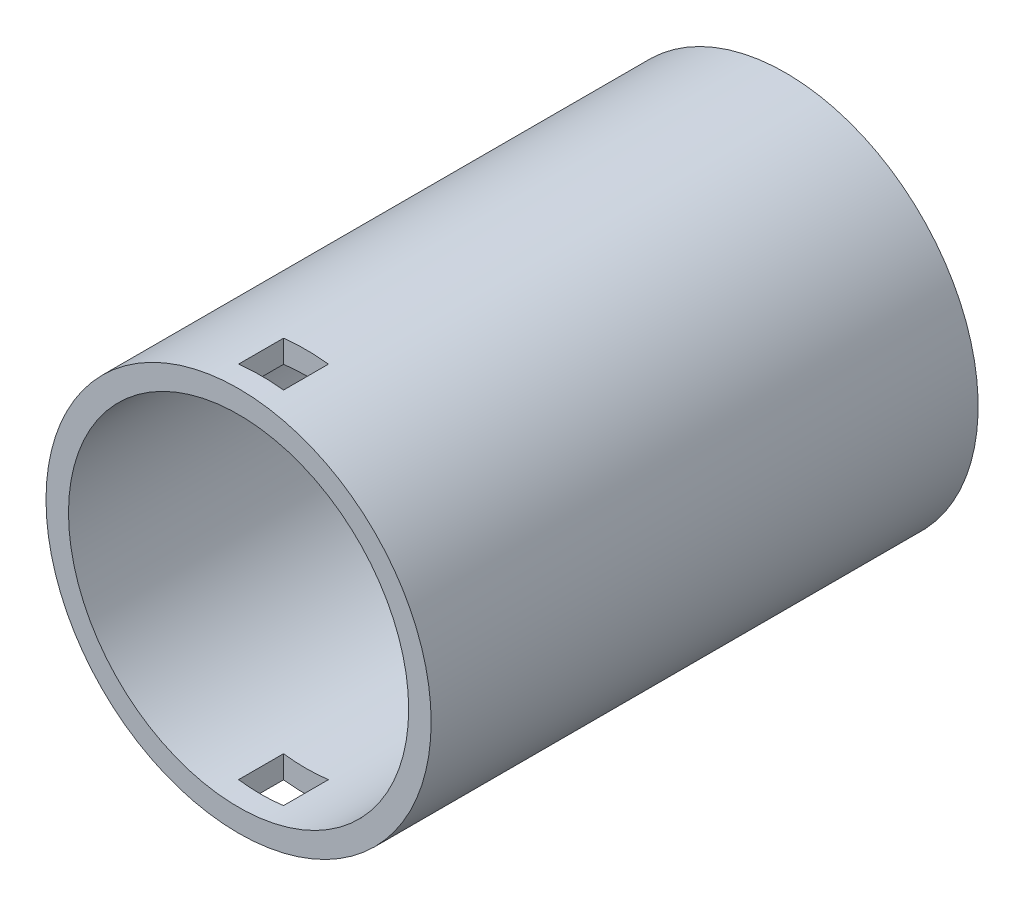
SolidWorks part; units mm, degrees
ref_plane "Plano frontal" through (0, 0, 0) normal (0, 0, 1) x (1, 0, 0)
ref_plane "Plano superior" through (0, 0, 0) normal (0, 1, 0) x (1, 0, 0)
ref_plane "Plano direito" through (0, 0, 0) normal (1, 0, 0) x (0, 0, -1)
sketch "Esboço1" plane through (0, 0, 0) normal (0, 0, 1) x (1, 0, 0)
  circle A0 centre (0, 0) radius 11.35
  circle A1 centre (0, 0) radius 12.85
  dimension "D1" = 1.5
extrude "Ressalto-extrusão1" add sketch "Esboço1" along normal blind 35
sketch "Esboço2" plane through (0, 0, 0) normal (0, 0, -1) x (-1, 0, 0)
  circle A1 centre (0, 0) radius 12.85
  circle A2 centre (0, 0) radius 12.85
  dimension "D1" = 0
extrude "Ressalto-extrusão2" add sketch "Esboço2" along normal blind 1.5
sketch "Esboço3" plane through (0, 0, 0) normal (0, 1, 0) x (1, 0, 0)
  line L0 (0, -35) -> (0, -32) construction
  line L1 (-12.85, -35) -> (12.85, -35) construction
  line L3 (-1.5, -30.5) -> (1.5, -30.5)
  line L4 (-1.5, -30.5) -> (-1.5, -33.5)
  line L5 (-1.5, -33.5) -> (1.5, -33.5)
  line L6 (1.5, -30.5) -> (1.5, -33.5)
  line L7 (-1.5, -30.5) -> (1.5, -33.5) construction
  line L8 (-1.5, -33.5) -> (1.5, -30.5) construction
  dimension "D1" = 3
extrude "Corte-extrusão1" cut sketch "Esboço3" against normal through all and the other way through all
